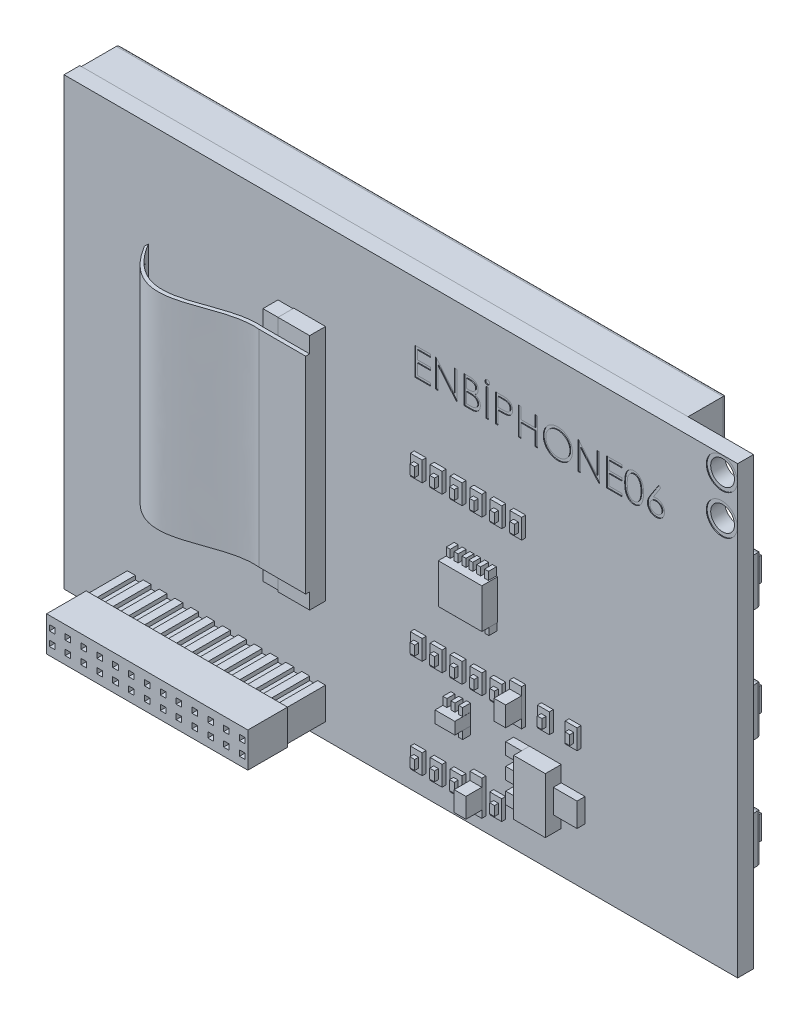
SolidWorks part; units mm, degrees
ref_plane "Front Plane" through (0, 0, 0) normal (0, 0, 1) x (1, 0, 0)
ref_plane "Top Plane" through (0, 0, 0) normal (0, 1, 0) x (1, 0, 0)
ref_plane "Right Plane" through (0, 0, 0) normal (1, 0, 0) x (0, 0, -1)
sketch "Sketch1" plane through (0, 0, 0) normal (0, 0, 1) x (1, 0, 0)
  line L0 (0, 0) -> (85.01, 0)
  line L1 (85.01, 0) -> (85.01, 56.21)
  line L2 (85.01, 56.21) -> (0, 56.21)
  line L3 (0, 56.21) -> (0, 0)
  dimension "D1" = 85.01
  dimension "D2" = 56.21
extrude "Boss-Extrude1" add sketch "Sketch1" along normal blind 2
sketch "Sketch2" plane through (0, 0, 2) normal (0, 0, 1) x (1, 0, 0)
  line L0 (85.01, 0) -> (85.01, 56.21) construction
  line L1 (85.01, 56.21) -> (0, 56.21) construction
  circle A1 centre (83.01, 54.21) radius 1.5
  circle A3 centre (83.01, 49.21) radius 1.5
  dimension "D4" = 3
  dimension "D6" = 3
  dimension "D2" = 2
  dimension "D3" = 2
  dimension "D5" = 5
extrude "Cut-Extrude1" cut sketch "Sketch2" against normal blind 2
sketch "Sketch4" plane through (0, 0, 2) normal (0, 0, 1) x (1, 0, 0)
  circle A0 centre (83.01, 54.21) radius 1.95
  circle A1 centre (83.01, 54.21) radius 1.5
  circle A2 centre (83.01, 49.21) radius 1.95
  circle A3 centre (83.01, 49.21) radius 1.5
  dimension "D1" = 3.9
  dimension "D2" = 3.9
extrude "Cut-Extrude7" cut sketch "Sketch4" against normal blind 0.1
sketch "Sketch5" plane through (0, 0, 0) normal (0, 0, -1) x (-1, 0, 0)
  circle A0 centre (-83.01, 54.21) radius 1.95
  circle A1 centre (-83.01, 49.21) radius 1.95
  circle A2 centre (-83.01, 54.21) radius 1.5
  circle A3 centre (-83.01, 49.21) radius 1.5
  dimension "D1" = 3.9
  dimension "D2" = 3.9
extrude "Cut-Extrude8" cut sketch "Sketch5" against normal blind 0.1
sketch "Sketch6" plane through (0, 0, 0) normal (0, 0, -1) x (-1, 0, 0)
  line L0 (-0.1, 56.11) -> (-0.1, 2.23)
  line L2 (-0.1, 2.23) -> (-76.65, 2.23)
  line L4 (-76.65, 2.23) -> (-76.65, 56.11)
  line L6 (-76.65, 56.11) -> (-0.1, 56.11)
  line L9 (-85.01, 56.21) -> (0, 56.21) construction
  line L10 (0, 56.21) -> (0, 0) construction
  line L11 (0, 0) -> (-85.01, 0) construction
  line L12 (-85.01, 0) -> (-85.01, 56.21) construction
  dimension "D1" = 0.1
  dimension "D2" = 0.1
  dimension "D3" = 2.23
  dimension "D4" = 8.36
extrude "Boss-Extrude2" add sketch "Sketch6" along normal blind 5
sketch "Sketch7" plane through (0, 0, -5) normal (0, 0, -1) x (-1, 0, 0)
  line L0 (-75.15, 54.71) -> (-1.5, 54.71)
  line L1 (-1.5, 54.71) -> (-1.5, 3.73)
  line L2 (-1.5, 3.73) -> (-75.15, 3.73)
  line L3 (-75.15, 3.73) -> (-75.15, 54.71)
  line L8 (-0.1, 56.11) -> (-76.65, 56.11) construction
  line L9 (-0.1, 2.23) -> (-0.1, 56.11) construction
  line L10 (-76.65, 2.23) -> (-0.1, 2.23) construction
  line L11 (-76.65, 56.11) -> (-76.65, 2.23) construction
  dimension "D1" = 1.4
  dimension "D2" = 1.4
  dimension "D3" = 1.5
  dimension "D4" = 1.5
extrude "Cut-Extrude9" cut sketch "Sketch7" against normal blind 0.1
fillet "Fillet1" radius 0.5 4 edges at (38.375, 2.23, -5) (76.65, 29.17, -5) (0.1, 29.17, -5) (38.375, 56.11, -5)
sketch "Sketch8" plane through (0, 0, 0) normal (0, 0, -1) x (-1, 0, 0)
  line L0 (-84.01, 10) -> (-81.01, 10)
  line L1 (-81.01, 10) -> (-81.01, 16)
  line L2 (-81.01, 16) -> (-84.01, 16)
  line L3 (-84.01, 16) -> (-84.01, 10)
  line L4 (-81.01, 24) -> (-84.01, 24)
  line L5 (-84.01, 24) -> (-84.01, 30)
  line L6 (-84.01, 30) -> (-81.01, 30)
  line L7 (-81.01, 30) -> (-81.01, 24)
  line L8 (-84.01, 44.21) -> (-84.01, 38.21)
  line L9 (-84.01, 38.21) -> (-81.01, 38.21)
  line L10 (-81.01, 38.21) -> (-81.01, 44.21)
  line L11 (-81.01, 44.21) -> (-84.01, 44.21)
  line L12 (0, 0) -> (-85.01, 0) construction
  line L13 (-85.01, 56.21) -> (0, 56.21) construction
  line L14 (-85.01, 0) -> (-85.01, 56.21) construction
  dimension "D1" = 6
  dimension "D2" = 6
  dimension "D3" = 6
  dimension "D4" = 10
  dimension "D5" = 12
  dimension "D6" = 8
  dimension "D7" = 1
  dimension "D8" = 1
  dimension "D9" = 3
  dimension "D10" = 3
  dimension "D11" = 3
extrude "Boss-Extrude3" add sketch "Sketch8" along normal blind 2
fillet "Fillet2" radius 0.5 12 edges at (81.01, 41.21, -2) (82.51, 38.21, -2) (84.01, 41.21, -2) (82.51, 44.21, -2) (82.51, 24, -2) (84.01, 27, -2) (82.51, 30, -2) (81.01, 27, -2) (82.51, 16, -2) (81.01, 13, -2) (82.51, 10, -2) (84.01, 13, -2)
sketch "Sketch9" plane through (0, 0, -2) normal (0, 0, -1) x (-1, 0, 0)
  line L0 (-83.01, 42.71) -> (-82.01, 42.71)
  line L1 (-82.01, 42.71) -> (-82.01, 39.71)
  line L2 (-82.01, 39.71) -> (-83.01, 39.71)
  line L3 (-83.01, 39.71) -> (-83.01, 42.71)
  line L4 (-83.51, 43.71) -> (-83.51, 38.71) construction
  line L5 (-83.51, 38.71) -> (-81.51, 38.71) construction
  line L6 (-83.01, 28.5) -> (-82.01, 28.5)
  line L7 (-82.01, 28.5) -> (-82.01, 25.5)
  line L8 (-82.01, 25.5) -> (-83.01, 25.5)
  line L9 (-83.01, 25.5) -> (-83.01, 28.5)
  line L10 (-83.51, 29.5) -> (-83.51, 24.5) construction
  line L11 (-81.51, 29.5) -> (-83.51, 29.5) construction
  line L12 (-83.01, 14.5) -> (-82.01, 14.5)
  line L13 (-82.01, 14.5) -> (-82.01, 11.5)
  line L14 (-82.01, 11.5) -> (-83.01, 11.5)
  line L15 (-83.01, 11.5) -> (-83.01, 14.5)
  line L16 (-83.51, 15.5) -> (-83.51, 10.5) construction
  line L17 (-81.51, 15.5) -> (-83.51, 15.5) construction
  point P6 (-82.51, 38.71)
  dimension "D1" = 1
  dimension "D2" = 3
  dimension "D3" = 0.5
  dimension "D4" = 1
  dimension "D5" = 1
  dimension "D6" = 3
  dimension "D7" = 0.5
  dimension "D8" = 1
  dimension "D9" = 1
  dimension "D10" = 3
  dimension "D11" = 0.5
  dimension "D12" = 1
extrude "Boss-Extrude4" add sketch "Sketch9" along normal blind 1
sketch "Sketch10" plane through (0, 0, 2) normal (0, 0, 1) x (1, 0, 0)
  line L0 (8, 2) -> (8, 6)
  line L1 (8, 2) -> (9, 2)
  line L2 (33, 6) -> (33, 2)
  line L3 (9, 2) -> (9, 2.5)
  line L5 (0, 56.21) -> (0, 0) construction
  line L6 (9, 2.5) -> (10, 2.5)
  line L7 (10, 2.5) -> (10, 2)
  line L8 (10, 2) -> (11, 2)
  line L9 (11, 2) -> (11, 2.5)
  line L10 (11, 2.5) -> (12, 2.5)
  line L11 (12, 2.5) -> (12, 2)
  line L12 (12, 2) -> (13, 2)
  line L13 (13, 2) -> (13, 2.5)
  line L14 (13, 2.5) -> (14, 2.5)
  line L15 (14, 2.5) -> (14, 2)
  line L16 (14, 2) -> (15, 2)
  line L17 (15, 2) -> (15, 2.5)
  line L18 (15, 2.5) -> (16, 2.5)
  line L19 (16, 2.5) -> (16, 2)
  line L20 (16, 2) -> (17, 2)
  line L21 (17, 2) -> (17, 2.5)
  line L22 (17, 2.5) -> (18, 2.5)
  line L23 (18, 2.5) -> (18, 2)
  line L24 (18, 2) -> (19, 2)
  line L25 (19, 2) -> (19, 2.5)
  line L26 (19, 2.5) -> (20, 2.5)
  line L27 (20, 2.5) -> (20, 2)
  line L28 (20, 2) -> (21, 2)
  line L29 (21, 2) -> (21, 2.5)
  line L30 (21, 2.5) -> (22, 2.5)
  line L31 (22, 2.5) -> (22, 2)
  line L32 (22, 2) -> (23, 2)
  line L33 (23, 2) -> (23, 2.5)
  line L34 (23, 2.5) -> (24, 2.5)
  line L35 (24, 2.5) -> (24, 2)
  line L36 (24, 2) -> (25, 2)
  line L37 (25, 2) -> (25, 2.5)
  line L38 (25, 2.5) -> (26, 2.5)
  line L39 (26, 2.5) -> (26, 2)
  line L40 (26, 2) -> (27, 2)
  line L41 (27, 2) -> (27, 2.5)
  line L42 (27, 2.5) -> (28, 2.5)
  line L43 (28, 2.5) -> (28, 2)
  line L44 (28, 2) -> (29, 2)
  line L45 (29, 2) -> (29, 2.5)
  line L46 (29, 2.5) -> (30, 2.5)
  line L47 (30, 2.5) -> (30, 2)
  line L48 (30, 2) -> (31, 2)
  line L49 (31, 2) -> (31, 2.5)
  line L50 (31, 2.5) -> (32, 2.5)
  line L51 (32, 2.5) -> (32, 2)
  line L52 (32, 2) -> (33, 2)
  line L54 (8, 4) -> (10, 4) construction
  line L55 (32, 5.5) -> (32, 6)
  line L56 (33, 2.5) -> (34, 2.5) [skipped]
  line L57 (34, 2.5) -> (34, 2) [skipped]
  line L58 (31, 5.5) -> (32, 5.5)
  line L59 (31, 6) -> (31, 5.5)
  line L60 (30, 6) -> (31, 6)
  line L61 (30, 5.5) -> (30, 6)
  line L62 (29, 5.5) -> (30, 5.5)
  line L63 (29, 6) -> (29, 5.5)
  line L64 (28, 6) -> (29, 6)
  line L65 (28, 5.5) -> (28, 6)
  line L66 (27, 5.5) -> (28, 5.5)
  line L67 (27, 6) -> (27, 5.5)
  line L68 (26, 6) -> (27, 6)
  line L69 (26, 5.5) -> (26, 6)
  line L70 (25, 5.5) -> (26, 5.5)
  line L71 (25, 6) -> (25, 5.5)
  line L72 (24, 6) -> (25, 6)
  line L73 (24, 5.5) -> (24, 6)
  line L74 (23, 5.5) -> (24, 5.5)
  line L75 (23, 6) -> (23, 5.5)
  line L76 (22, 6) -> (23, 6)
  line L77 (22, 5.5) -> (22, 6)
  line L78 (21, 5.5) -> (22, 5.5)
  line L79 (21, 6) -> (21, 5.5)
  line L80 (20, 6) -> (21, 6)
  line L81 (20, 5.5) -> (20, 6)
  line L82 (19, 5.5) -> (20, 5.5)
  line L83 (19, 6) -> (19, 5.5)
  line L84 (18, 6) -> (19, 6)
  line L85 (18, 5.5) -> (18, 6)
  line L86 (17, 5.5) -> (18, 5.5)
  line L87 (17, 6) -> (17, 5.5)
  line L88 (16, 6) -> (17, 6)
  line L89 (16, 5.5) -> (16, 6)
  line L90 (15, 5.5) -> (16, 5.5)
  line L91 (15, 6) -> (15, 5.5)
  line L92 (14, 6) -> (15, 6)
  line L93 (14, 5.5) -> (14, 6)
  line L94 (13, 5.5) -> (14, 5.5)
  line L95 (13, 6) -> (13, 5.5)
  line L96 (12, 6) -> (13, 6)
  line L97 (12, 5.5) -> (12, 6)
  line L98 (11, 5.5) -> (12, 5.5)
  line L99 (11, 6) -> (11, 5.5)
  line L100 (10, 6) -> (11, 6)
  line L101 (10, 5.5) -> (10, 6)
  line L102 (9, 5.5) -> (10, 5.5)
  line L103 (9, 6) -> (9, 5.5)
  line L104 (8, 6) -> (9, 6)
  line L105 (32, 6) -> (33, 6)
  line L107 (33, 2) -> (33, 2.5) [skipped]
  dimension "D2" = 8
  dimension "D3" = 25
  dimension "D4" = 4
  dimension "D5" = 1
  dimension "D6" = 0.5
  dimension "D7" = 0.5
  dimension "D8" = 13
extrude "Boss-Extrude5" add sketch "Sketch10" along normal blind 5
sketch "Sketch11" plane through (0, 0, 7) normal (0, 0, 1) x (1, 0, 0)
  line L0 (7.8, 6.2) -> (7.8, 1.8)
  line L1 (7.8, 1.8) -> (33.2, 1.8)
  line L2 (33.2, 1.8) -> (33.2, 6.2)
  line L3 (33.2, 6.2) -> (7.8, 6.2)
  line L4 (8, 6) -> (8, 2) construction
  line L5 (33, 2) -> (33, 6) construction
  line L6 (33, 6) -> (32, 6) construction
  line L7 (32, 2) -> (33, 2) construction
  line L8 (8.15, 5.2) -> (8.15, 4.5)
  line L9 (8.15, 4.5) -> (8.85, 4.5)
  line L10 (8.85, 4.5) -> (8.85, 5.2)
  line L11 (8.85, 5.2) -> (8.15, 5.2)
  line L12 (7.8, 4) -> (10.85, 4) construction
  line L13 (10.85, 5.2) -> (10.15, 5.2)
  line L14 (10.15, 5.2) -> (10.15, 4.5)
  line L15 (10.15, 4.5) -> (10.85, 4.5)
  line L16 (10.85, 4.5) -> (10.85, 5.2)
  line L17 (32.85, 3.5) -> (32.85, 2.8)
  line L18 (12.85, 5.2) -> (12.15, 5.2)
  line L19 (12.15, 5.2) -> (12.15, 4.5)
  line L20 (12.15, 4.5) -> (12.85, 4.5)
  line L21 (12.85, 4.5) -> (12.85, 5.2)
  line L22 (32.15, 3.5) -> (32.85, 3.5)
  line L23 (14.85, 5.2) -> (14.15, 5.2)
  line L24 (14.15, 5.2) -> (14.15, 4.5)
  line L25 (14.15, 4.5) -> (14.85, 4.5)
  line L26 (14.85, 4.5) -> (14.85, 5.2)
  line L27 (32.15, 2.8) -> (32.15, 3.5)
  line L28 (16.85, 5.2) -> (16.15, 5.2)
  line L29 (16.15, 5.2) -> (16.15, 4.5)
  line L30 (16.15, 4.5) -> (16.85, 4.5)
  line L31 (16.85, 4.5) -> (16.85, 5.2)
  line L32 (32.85, 2.8) -> (32.15, 2.8)
  line L33 (18.85, 5.2) -> (18.15, 5.2)
  line L34 (18.15, 5.2) -> (18.15, 4.5)
  line L35 (18.15, 4.5) -> (18.85, 4.5)
  line L36 (18.85, 4.5) -> (18.85, 5.2)
  line L37 (30.85, 3.5) -> (30.85, 2.8)
  line L38 (20.85, 5.2) -> (20.15, 5.2)
  line L39 (20.15, 5.2) -> (20.15, 4.5)
  line L40 (20.15, 4.5) -> (20.85, 4.5)
  line L41 (20.85, 4.5) -> (20.85, 5.2)
  line L42 (30.15, 3.5) -> (30.85, 3.5)
  line L43 (22.85, 5.2) -> (22.15, 5.2)
  line L44 (22.15, 5.2) -> (22.15, 4.5)
  line L45 (22.15, 4.5) -> (22.85, 4.5)
  line L46 (22.85, 4.5) -> (22.85, 5.2)
  line L47 (30.15, 2.8) -> (30.15, 3.5)
  line L48 (24.85, 5.2) -> (24.15, 5.2)
  line L49 (24.15, 5.2) -> (24.15, 4.5)
  line L50 (24.15, 4.5) -> (24.85, 4.5)
  line L51 (24.85, 4.5) -> (24.85, 5.2)
  line L52 (30.85, 2.8) -> (30.15, 2.8)
  line L53 (26.85, 5.2) -> (26.15, 5.2)
  line L54 (26.15, 5.2) -> (26.15, 4.5)
  line L55 (26.15, 4.5) -> (26.85, 4.5)
  line L56 (26.85, 4.5) -> (26.85, 5.2)
  line L57 (28.85, 3.5) -> (28.85, 2.8)
  line L58 (28.85, 5.2) -> (28.15, 5.2)
  line L59 (28.15, 5.2) -> (28.15, 4.5)
  line L60 (28.15, 4.5) -> (28.85, 4.5)
  line L61 (28.85, 4.5) -> (28.85, 5.2)
  line L62 (28.15, 3.5) -> (28.85, 3.5)
  line L63 (30.85, 5.2) -> (30.15, 5.2)
  line L64 (30.15, 5.2) -> (30.15, 4.5)
  line L65 (30.15, 4.5) -> (30.85, 4.5)
  line L66 (30.85, 4.5) -> (30.85, 5.2)
  line L67 (28.15, 2.8) -> (28.15, 3.5)
  line L68 (32.85, 5.2) -> (32.15, 5.2)
  line L69 (32.15, 5.2) -> (32.15, 4.5)
  line L70 (32.15, 4.5) -> (32.85, 4.5)
  line L71 (32.85, 4.5) -> (32.85, 5.2)
  line L72 (39.2, 6.2) -> (13.8, 6.2) [skipped]
  line L73 (41.2, 6.2) -> (15.8, 6.2) [skipped]
  line L74 (43.2, 6.2) -> (17.8, 6.2) [skipped]
  line L75 (45.2, 6.2) -> (19.8, 6.2) [skipped]
  line L76 (47.2, 6.2) -> (21.8, 6.2) [skipped]
  line L77 (49.2, 6.2) -> (23.8, 6.2) [skipped]
  line L78 (51.2, 6.2) -> (25.8, 6.2) [skipped]
  line L79 (53.2, 6.2) -> (27.8, 6.2) [skipped]
  line L80 (55.2, 6.2) -> (29.8, 6.2) [skipped]
  line L81 (57.2, 6.2) -> (31.8, 6.2) [skipped]
  line L82 (37.2, 6.2) -> (11.8, 6.2) [skipped]
  line L83 (35.2, 6.2) -> (9.8, 6.2) [skipped]
  line L84 (28.85, 2.8) -> (28.15, 2.8)
  line L85 (26.85, 3.5) -> (26.85, 2.8)
  line L86 (26.15, 3.5) -> (26.85, 3.5)
  line L87 (26.15, 2.8) -> (26.15, 3.5)
  line L88 (26.85, 2.8) -> (26.15, 2.8)
  line L89 (24.85, 3.5) -> (24.85, 2.8)
  line L90 (24.15, 3.5) -> (24.85, 3.5)
  line L91 (24.15, 2.8) -> (24.15, 3.5)
  line L92 (24.85, 2.8) -> (24.15, 2.8)
  line L93 (22.85, 3.5) -> (22.85, 2.8)
  line L94 (22.15, 3.5) -> (22.85, 3.5)
  line L95 (22.15, 2.8) -> (22.15, 3.5)
  line L96 (22.85, 2.8) -> (22.15, 2.8)
  line L97 (20.85, 3.5) -> (20.85, 2.8)
  line L98 (20.15, 3.5) -> (20.85, 3.5)
  line L99 (20.15, 2.8) -> (20.15, 3.5)
  line L100 (20.85, 2.8) -> (20.15, 2.8)
  line L101 (18.85, 3.5) -> (18.85, 2.8)
  line L102 (18.15, 3.5) -> (18.85, 3.5)
  line L103 (18.15, 2.8) -> (18.15, 3.5)
  line L104 (18.85, 2.8) -> (18.15, 2.8)
  line L105 (16.85, 3.5) -> (16.85, 2.8)
  line L106 (16.15, 3.5) -> (16.85, 3.5)
  line L107 (16.15, 2.8) -> (16.15, 3.5)
  line L108 (16.85, 2.8) -> (16.15, 2.8)
  line L109 (14.85, 3.5) -> (14.85, 2.8)
  line L110 (14.15, 3.5) -> (14.85, 3.5)
  line L111 (14.15, 2.8) -> (14.15, 3.5)
  line L112 (14.85, 2.8) -> (14.15, 2.8)
  line L113 (12.85, 3.5) -> (12.85, 2.8)
  line L114 (12.15, 3.5) -> (12.85, 3.5)
  line L115 (12.15, 2.8) -> (12.15, 3.5)
  line L116 (12.85, 2.8) -> (12.15, 2.8)
  line L117 (10.85, 3.5) -> (10.85, 2.8)
  line L118 (10.15, 3.5) -> (10.85, 3.5)
  line L119 (10.15, 2.8) -> (10.15, 3.5)
  line L120 (10.85, 2.8) -> (10.15, 2.8)
  line L121 (8.85, 2.8) -> (8.15, 2.8)
  line L122 (8.85, 3.5) -> (8.85, 2.8)
  line L123 (8.15, 3.5) -> (8.85, 3.5)
  line L124 (8.15, 2.8) -> (8.15, 3.5)
  dimension "D1" = 0.2
  dimension "D2" = 0.2
  dimension "D3" = 0.2
  dimension "D4" = 0.2
  dimension "D5" = 0.7
  dimension "D6" = 0.7
  dimension "D7" = 0.35
  dimension "D8" = 1
  dimension "D9" = 13
extrude "Boss-Extrude6" add sketch "Sketch11" along normal blind 5
sketch "Sketch13" plane through (0, 0, 2) normal (0, 0, 1) x (1, 0, 0)
  line L0 (44.2, 5.2) -> (44.2, 2.7)
  line L1 (44.2, 2.7) -> (45.7, 2.7)
  line L2 (45.7, 2.7) -> (45.7, 5.2)
  line L3 (45.7, 5.2) -> (44.2, 5.2)
  line L4 (33.2, 6.2) -> (7.8, 6.2) construction
  line L5 (53.2275, 37.2171) -> (51.7275, 37.2171)
  line L6 (33.2, 1.8) -> (33.2, 6.2) construction
  line L7 (48.2138, 5.2) -> (46.7138, 5.2)
  line L8 (46.7138, 5.2) -> (46.7138, 2.7)
  line L9 (46.7138, 2.7) -> (48.2138, 2.7)
  line L10 (48.2138, 2.7) -> (48.2138, 5.2)
  line L11 (50.7275, 5.2) -> (49.2275, 5.2)
  line L12 (49.2275, 5.2) -> (49.2275, 2.7)
  line L13 (49.2275, 2.7) -> (50.7275, 2.7)
  line L14 (50.7275, 2.7) -> (50.7275, 5.2)
  line L15 (51.7275, 6.2) -> (51.7275, 1.8)
  line L16 (51.7275, 1.8) -> (53.2275, 1.8)
  line L17 (53.2275, 1.8) -> (53.2275, 6.2)
  line L18 (53.2275, 6.2) -> (51.7275, 6.2)
  line L19 (7.8, 1.8) -> (33.2, 1.8) construction
  line L20 (54.2275, 5.2) -> (54.2275, 2.7)
  line L21 (54.2275, 2.7) -> (55.7275, 2.7)
  line L22 (55.7275, 2.7) -> (55.7275, 5.2)
  line L23 (55.7275, 5.2) -> (54.2275, 5.2)
  line L24 (49.2275, 15.2) -> (50.7275, 15.2)
  line L25 (48.2138, 15.2) -> (48.2138, 17.7)
  line L26 (45.7, 15.2) -> (45.7, 17.7)
  line L27 (50.7275, 15.2) -> (50.7275, 17.7)
  line L28 (44.2, 17.7) -> (44.2, 15.2)
  line L29 (50.7275, 17.7) -> (49.2275, 17.7)
  line L30 (46.7138, 17.7) -> (46.7138, 15.2)
  line L31 (48.2138, 17.7) -> (46.7138, 17.7)
  line L32 (44.2, 15.2) -> (45.7, 15.2)
  line L33 (49.2275, 17.7) -> (49.2275, 15.2)
  line L34 (45.7, 17.7) -> (44.2, 17.7)
  line L35 (46.7138, 15.2) -> (48.2138, 15.2)
  line L36 (51.7275, 15.2) -> (53.2275, 15.2)
  line L37 (55.7413, 15.2) -> (55.7413, 17.7)
  line L38 (54.2413, 15.2) -> (55.7413, 15.2)
  line L39 (53.2275, 17.7) -> (51.7275, 17.7)
  line L40 (51.7275, 17.7) -> (51.7275, 15.2)
  line L41 (53.2275, 15.2) -> (53.2275, 17.7)
  line L42 (55.7413, 17.7) -> (54.2413, 17.7)
  line L43 (54.2413, 17.7) -> (54.2413, 15.2)
  line L44 (56.7413, 18.7) -> (56.7413, 14.0831)
  line L45 (58.2413, 14.0831) -> (58.2413, 18.7)
  line L46 (56.7413, 14.0831) -> (58.2413, 14.0831)
  line L47 (58.2413, 18.7) -> (56.7413, 18.7)
  line L48 (61.7413, 17.7) -> (60.2413, 17.7)
  line L49 (61.7413, 15.2) -> (61.7413, 17.7)
  line L50 (60.2413, 17.7) -> (60.2413, 15.2)
  line L51 (60.2413, 15.2) -> (61.7413, 15.2)
  line L52 (65.2413, 15.2) -> (65.2413, 17.7)
  line L53 (65.2413, 17.7) -> (63.7413, 17.7)
  line L54 (63.7413, 15.2) -> (65.2413, 15.2)
  line L55 (63.7413, 17.7) -> (63.7413, 15.2)
  line L56 (54.2413, 37.2171) -> (54.2413, 34.7171)
  line L57 (55.7413, 34.7171) -> (55.7413, 37.2171)
  line L58 (54.2413, 34.7171) -> (55.7413, 34.7171)
  line L59 (51.7275, 34.7171) -> (53.2275, 34.7171)
  line L60 (46.7138, 37.2171) -> (46.7138, 34.7171)
  line L61 (48.2138, 34.7171) -> (48.2138, 37.2171)
  line L62 (55.7413, 37.2171) -> (54.2413, 37.2171)
  line L63 (50.7275, 34.7171) -> (50.7275, 37.2171)
  line L64 (44.2, 34.7) -> (45.7, 34.7)
  line L65 (50.7275, 37.2171) -> (49.2275, 37.2171)
  line L66 (45.7, 37.2) -> (44.2, 37.2)
  line L67 (51.7275, 37.2171) -> (51.7275, 34.7171)
  line L68 (46.7138, 34.7171) -> (48.2138, 34.7171)
  line L69 (49.2275, 34.7171) -> (50.7275, 34.7171)
  line L70 (53.2275, 34.7171) -> (53.2275, 37.2171)
  line L71 (45.7, 34.7) -> (45.7, 37.2)
  line L72 (48.2138, 37.2171) -> (46.7138, 37.2171)
  line L73 (44.2, 37.2) -> (44.2, 34.7)
  line L74 (49.2275, 37.2171) -> (49.2275, 34.7171)
  line L75 (58.2551, 34.7171) -> (58.2551, 37.2171)
  line L76 (58.2551, 37.2171) -> (56.7551, 37.2171)
  line L77 (56.7551, 37.2171) -> (56.7551, 34.7171)
  line L78 (56.7551, 34.7171) -> (58.2551, 34.7171)
  dimension "D1" = 1.5
  dimension "D2" = 2.5
  dimension "D3" = 1
  dimension "D4" = 11
  dimension "D6" = 1.5
  dimension "D7" = 1
  dimension "D8" = 0
  dimension "D9" = 0
  dimension "D10" = 1.5
  dimension "D11" = 2.5
  dimension "D12" = 1
  dimension "D13" = 2.5
  dimension "D14" = 1
  dimension "D15" = 1
  dimension "D16" = 2
  dimension "D17" = 2
  dimension "D18" = 10
  dimension "D19" = 17
  dimension "D5" = 3
extrude "Boss-Extrude7" add sketch "Sketch13" along normal blind 0.5
sketch "Sketch16" plane through (0, 0, 2.5) normal (0, 0, 1) x (1, 0, 0)
  line L0 (44.65, 4.5) -> (44.65, 3.3)
  line L1 (44.65, 3.3) -> (45.25, 3.3)
  line L2 (45.25, 3.3) -> (45.25, 4.5)
  line L3 (45.25, 4.5) -> (44.65, 4.5)
  line L4 (44.2, 5.2) -> (44.2, 2.7) construction
  line L5 (44.2, 2.7) -> (45.7, 2.7) construction
  line L6 (47.15, 3.3) -> (47.75, 3.3)
  line L7 (47.75, 3.3) -> (47.75, 4.5)
  line L8 (47.15, 4.5) -> (47.15, 3.3)
  line L9 (47.75, 4.5) -> (47.15, 4.5)
  line L10 (49.65, 3.3) -> (50.25, 3.3)
  line L11 (50.25, 3.3) -> (50.25, 4.5)
  line L12 (49.65, 4.5) -> (49.65, 3.3)
  line L13 (50.25, 4.5) -> (49.65, 4.5)
  line L14 (55.3202, 15.8) -> (55.3202, 17)
  line L15 (54.7202, 17) -> (54.7202, 15.8)
  line L16 (45.25, 17) -> (44.65, 17)
  line L17 (49.65, 15.8) -> (50.25, 15.8)
  line L18 (54.7202, 3.3) -> (55.3202, 3.3)
  line L19 (55.3202, 4.5) -> (54.7202, 4.5)
  line L20 (55.3202, 3.3) -> (55.3202, 4.5)
  line L21 (54.7202, 4.5) -> (54.7202, 3.3)
  line L22 (47.75, 15.8) -> (47.75, 17)
  line L23 (50.25, 17) -> (49.65, 17)
  line L24 (47.75, 17) -> (47.15, 17)
  line L25 (55.3202, 17) -> (54.7202, 17)
  line L26 (44.65, 17) -> (44.65, 15.8)
  line L27 (44.65, 15.8) -> (45.25, 15.8)
  line L28 (45.25, 15.8) -> (45.25, 17)
  line L29 (49.65, 17) -> (49.65, 15.8)
  line L30 (47.15, 15.8) -> (47.75, 15.8)
  line L31 (50.25, 15.8) -> (50.25, 17)
  line L32 (47.15, 17) -> (47.15, 15.8)
  line L33 (54.7202, 15.8) -> (55.3202, 15.8)
  line L34 (52.75, 15.8) -> (52.75, 17)
  line L35 (52.15, 15.8) -> (52.75, 15.8)
  line L36 (52.75, 17) -> (52.15, 17)
  line L37 (52.15, 17) -> (52.15, 15.8)
  line L38 (60.7202, 17) -> (60.7202, 15.8)
  line L39 (61.3202, 17) -> (60.7202, 17)
  line L40 (60.7202, 15.8) -> (61.3202, 15.8)
  line L41 (61.3202, 15.8) -> (61.3202, 17)
  line L42 (64.2202, 17) -> (64.2202, 15.8)
  line L43 (64.8202, 17) -> (64.2202, 17)
  line L44 (64.2202, 15.8) -> (64.8202, 15.8)
  line L45 (64.8202, 15.8) -> (64.8202, 17)
  line L46 (55.3202, 36.5) -> (54.7202, 36.5)
  line L47 (52.15, 36.5) -> (52.15, 35.3)
  line L48 (55.3202, 35.3) -> (55.3202, 36.5)
  line L49 (52.75, 36.5) -> (52.15, 36.5)
  line L50 (44.65, 36.5) -> (44.65, 35.3)
  line L51 (45.25, 36.5) -> (44.65, 36.5)
  line L52 (49.65, 35.3) -> (50.25, 35.3)
  line L53 (54.7202, 35.3) -> (55.3202, 35.3)
  line L54 (47.75, 36.5) -> (47.15, 36.5)
  line L55 (47.15, 35.3) -> (47.75, 35.3)
  line L56 (52.75, 35.3) -> (52.75, 36.5)
  line L57 (52.15, 35.3) -> (52.75, 35.3)
  line L58 (45.25, 35.3) -> (45.25, 36.5)
  line L59 (44.65, 35.3) -> (45.25, 35.3)
  line L60 (54.7202, 36.5) -> (54.7202, 35.3)
  line L61 (50.25, 36.5) -> (49.65, 36.5)
  line L62 (47.15, 36.5) -> (47.15, 35.3)
  line L63 (50.25, 35.3) -> (50.25, 36.5)
  line L64 (47.75, 35.3) -> (47.75, 36.5)
  line L65 (49.65, 36.5) -> (49.65, 35.3)
  line L66 (57.8339, 36.5) -> (57.2339, 36.5)
  line L67 (57.2339, 35.3) -> (57.8339, 35.3)
  line L68 (57.2339, 36.5) -> (57.2339, 35.3)
  line L69 (57.8339, 35.3) -> (57.8339, 36.5)
  dimension "D1" = 0.6
  dimension "D2" = 1.2
  dimension "D3" = 0.45
  dimension "D4" = 0.6
  dimension "D5" = 3
extrude "Boss-Extrude8" add sketch "Sketch16" along normal blind 0.5
sketch "Sketch17" plane through (0, 0, 2.5) normal (0, 0, 1) x (1, 0, 0)
  line L0 (51.7375, 5.2) -> (53.2175, 5.2)
  line L3 (53.2175, 5.2) -> (53.2175, 2.7)
  line L5 (53.2175, 2.7) -> (51.7375, 2.7)
  line L7 (51.7375, 2.7) -> (51.7375, 5.2)
  line L8 (51.7275, 6.2) -> (51.7275, 1.8) construction
  line L9 (53.2275, 1.8) -> (53.2275, 6.2) construction
  line L10 (58.2313, 15.2) -> (56.7513, 15.2)
  line L11 (58.2313, 17.7) -> (58.2313, 15.2)
  line L12 (56.7513, 15.2) -> (56.7513, 17.7)
  line L13 (56.7513, 17.7) -> (58.2313, 17.7)
  dimension "D1" = 0.01
  dimension "D2" = 0.01
extrude "Boss-Extrude9" add sketch "Sketch17" along normal blind 2
sketch "Sketch19" plane through (0, 0, 2) normal (0, 0, 1) x (1, 0, 0)
  line L0 (58.7413, 5.2) -> (58.7413, 12.2)
  line L1 (58.7413, 12.2) -> (62.7413, 12.2)
  line L2 (62.7413, 12.2) -> (62.7413, 5.2)
  line L3 (62.7413, 5.2) -> (58.7413, 5.2)
  line L4 (58.2413, 14.0831) -> (58.2413, 18.7) construction
  line L5 (48.8163, 12.2) -> (51.3163, 12.2)
  line L6 (51.3163, 12.2) -> (51.3163, 10.7)
  line L7 (51.3163, 10.7) -> (48.8163, 10.7)
  line L8 (48.8163, 10.7) -> (48.8163, 12.2)
  line L9 (49.2275, 28.7171) -> (49.2275, 23.7171)
  line L10 (49.2275, 23.7171) -> (54.7275, 23.7171)
  line L11 (54.7275, 23.7171) -> (54.7275, 28.7171)
  line L12 (54.7275, 28.7171) -> (49.2275, 28.7171)
  line L13 (49.2275, 34.7171) -> (50.7275, 34.7171) construction
  dimension "D1" = 4
  dimension "D2" = 0.5
  dimension "D3" = 7
  dimension "D4" = 1.5
  dimension "D5" = 2.5
  dimension "D6" = 5.5
  dimension "D7" = 5
  dimension "D8" = 6
extrude "Boss-Extrude10" add sketch "Sketch19" along normal blind 2
sketch "Sketch21" plane through (0, 0, 2) normal (0, 0, 1) x (1, 0, 0)
  line L0 (48.8263, 12.2) -> (48.8263, 13.2)
  line L1 (51.3163, 12.2) -> (48.8163, 12.2) construction
  line L2 (48.8263, 13.2) -> (49.3263, 13.2)
  line L3 (49.3263, 13.2) -> (49.3263, 12.2)
  line L4 (49.3263, 12.2) -> (48.8263, 12.2)
  line L5 (48.8163, 12.2) -> (48.8163, 10.7) construction
  line L6 (50.3263, 13.2) -> (50.3263, 12.2)
  line L7 (49.8263, 13.2) -> (50.3263, 13.2)
  line L8 (49.8263, 12.2) -> (49.8263, 13.2)
  line L9 (50.3263, 12.2) -> (49.8263, 12.2)
  line L11 (51.3063, 12.2) -> (50.8063, 12.2)
  line L12 (50.8063, 12.2) -> (50.8063, 13.2)
  line L13 (50.8063, 13.2) -> (51.3063, 13.2)
  line L14 (51.3063, 13.2) -> (51.3063, 12.2)
  line L15 (51.3163, 10.7) -> (51.3163, 12.2) construction
  line L16 (48.8163, 11.45) -> (50.8937, 11.45) construction
  line L17 (51.3063, 9.7) -> (51.3063, 10.7)
  line L18 (50.8063, 9.7) -> (51.3063, 9.7)
  line L19 (50.8063, 10.7) -> (50.8063, 9.7)
  line L20 (51.3063, 10.7) -> (50.8063, 10.7)
  line L21 (50.3263, 10.7) -> (49.8263, 10.7)
  line L22 (49.8263, 10.7) -> (49.8263, 9.7)
  line L23 (49.8263, 9.7) -> (50.3263, 9.7)
  line L24 (50.3263, 9.7) -> (50.3263, 10.7)
  line L25 (49.3263, 10.7) -> (48.8263, 10.7)
  line L26 (49.3263, 9.7) -> (49.3263, 10.7)
  line L27 (48.8263, 9.7) -> (49.3263, 9.7)
  line L28 (48.8263, 10.7) -> (48.8263, 9.7)
  line L29 (50.2375, 29.7171) -> (50.7375, 29.7171)
  line L30 (49.2375, 28.7171) -> (49.2375, 29.7171)
  line L31 (51.2175, 29.7171) -> (51.7175, 29.7171)
  line L32 (50.7375, 29.7171) -> (50.7375, 28.7171)
  line L33 (51.7175, 29.7171) -> (51.7175, 28.7171)
  line L34 (49.7375, 28.7171) -> (49.2375, 28.7171)
  line L35 (49.2375, 29.7171) -> (49.7375, 29.7171)
  line L36 (51.7175, 28.7171) -> (51.2175, 28.7171)
  line L37 (49.7375, 29.7171) -> (49.7375, 28.7171)
  line L38 (50.7375, 28.7171) -> (50.2375, 28.7171)
  line L39 (50.2375, 28.7171) -> (50.2375, 29.7171)
  line L40 (51.2175, 28.7171) -> (51.2175, 29.7171)
  line L41 (53.0814, 29.7171) -> (53.5814, 29.7171)
  line L42 (52.0814, 28.7171) -> (52.0814, 29.7171)
  line L43 (54.0614, 29.7171) -> (54.5614, 29.7171)
  line L44 (53.5814, 29.7171) -> (53.5814, 28.7171)
  line L45 (54.5614, 29.7171) -> (54.5614, 28.7171)
  line L46 (52.5814, 28.7171) -> (52.0814, 28.7171)
  line L47 (52.0814, 29.7171) -> (52.5814, 29.7171)
  line L48 (54.5614, 28.7171) -> (54.0614, 28.7171)
  line L49 (52.5814, 29.7171) -> (52.5814, 28.7171)
  line L50 (53.5814, 28.7171) -> (53.0814, 28.7171)
  line L51 (53.0814, 28.7171) -> (53.0814, 29.7171)
  line L52 (54.0614, 28.7171) -> (54.0614, 29.7171)
  line L53 (51.7713, 23.715) -> (51.7713, 22.715)
  line L54 (52.1351, 22.715) -> (52.1351, 23.715)
  line L55 (53.1351, 22.715) -> (53.1351, 23.715)
  line L56 (51.7713, 22.715) -> (51.2713, 22.715)
  line L57 (54.1151, 23.715) -> (54.6151, 23.715)
  line L58 (52.1351, 23.715) -> (52.6351, 23.715)
  line L59 (53.1351, 23.715) -> (53.6351, 23.715)
  line L60 (53.6351, 23.715) -> (53.6351, 22.715)
  line L61 (50.7913, 22.715) -> (50.2913, 22.715)
  line L62 (49.7913, 22.715) -> (49.2913, 22.715)
  line L63 (49.2913, 23.715) -> (49.7913, 23.715)
  line L64 (53.6351, 22.715) -> (53.1351, 22.715)
  line L65 (50.2913, 23.715) -> (50.7913, 23.715)
  line L66 (49.2913, 22.715) -> (49.2913, 23.715)
  line L67 (52.6351, 23.715) -> (52.6351, 22.715)
  line L68 (49.7913, 23.715) -> (49.7913, 22.715)
  line L69 (50.2913, 22.715) -> (50.2913, 23.715)
  line L70 (54.6151, 23.715) -> (54.6151, 22.715)
  line L71 (54.6151, 22.715) -> (54.1151, 22.715)
  line L72 (50.7913, 23.715) -> (50.7913, 22.715)
  line L73 (52.6351, 22.715) -> (52.1351, 22.715)
  line L74 (54.1151, 22.715) -> (54.1151, 23.715)
  line L75 (51.2713, 23.715) -> (51.7713, 23.715)
  line L76 (51.2713, 22.715) -> (51.2713, 23.715)
  line L77 (62.7413, 10.2) -> (65.7413, 10.2)
  line L78 (62.7413, 5.2) -> (62.7413, 12.2) construction
  line L79 (65.7413, 10.2) -> (65.7413, 7.2)
  line L80 (65.7413, 7.2) -> (62.7413, 7.2)
  line L81 (62.7413, 7.2) -> (62.7413, 10.2)
  line L82 (58.7413, 12.19) -> (56.7413, 12.19)
  line L83 (58.7413, 12.2) -> (58.7413, 5.2) construction
  line L84 (56.7413, 12.19) -> (56.7413, 10.69)
  line L85 (56.7413, 10.69) -> (58.7413, 10.69)
  line L86 (58.7413, 10.69) -> (58.7413, 12.19)
  line L87 (62.7413, 12.2) -> (58.7413, 12.2) construction
  line L88 (62.7413, 12.2) -> (58.7413, 12.2) construction
  line L89 (58.7413, 9.49) -> (56.7413, 9.49)
  line L90 (56.7413, 9.49) -> (56.7413, 7.99)
  line L91 (56.7413, 7.99) -> (58.7413, 7.99)
  line L92 (58.7413, 7.99) -> (58.7413, 9.49)
  line L93 (58.7413, 6.79) -> (56.7413, 6.79)
  line L94 (56.7413, 6.79) -> (56.7413, 5.29)
  line L95 (56.7413, 5.29) -> (58.7413, 5.29)
  line L96 (58.7413, 5.29) -> (58.7413, 6.79)
  dimension "D1" = 0.01
  dimension "D2" = 0.5
  dimension "D3" = 1
  dimension "D5" = 0.01
  dimension "D6" = 0.5
  dimension "D7" = 1
  dimension "D8" = 0.5
  dimension "D9" = 1
  dimension "D10" = 0.5
  dimension "D11" = 1
  dimension "D12" = 0.5
  dimension "D13" = 1
  dimension "D14" = 0.5
  dimension "D15" = 0.01
  dimension "D16" = 1.5
  dimension "D17" = 2
  dimension "D18" = 3
  dimension "D19" = 3
  dimension "D20" = 2
  dimension "D4" = 2
  dimension "D21" = 3
extrude "Boss-Extrude12" add sketch "Sketch21" along normal blind 1
sketch "Sketch22" plane through (0, 0, 2) normal (0, 0, 1) x (1, 0, 0)
  line L0 (33, 15.2) -> (33, 45.2)
  line L1 (33, 45.2) -> (29, 45.2)
  line L2 (29, 45.2) -> (29, 15.2)
  line L3 (29, 15.2) -> (33, 15.2)
  dimension "D1" = 4
  dimension "D2" = 30
extrude "Boss-Extrude13" add sketch "Sketch22" along normal blind 2
sketch "Sketch23" plane through (0, 0, 2) normal (0, 0, 1) x (1, 0, 0)
  line L0 (29, 45.1) -> (27, 45.1)
  line L1 (29, 45.2) -> (29, 15.2) construction
  line L2 (27, 45.1) -> (27, 15.3)
  line L3 (27, 15.3) -> (29, 15.3)
  line L4 (29, 15.3) -> (29, 45.1)
  line L5 (33, 45.2) -> (29, 45.2) construction
  line L6 (29, 15.2) -> (33, 15.2) construction
  dimension "D1" = 0.1
  dimension "D2" = 0.1
  dimension "D3" = 2
extrude "Boss-Extrude14" add sketch "Sketch23" along normal blind 1.9
sketch "Sketch25" plane through (0, 0, 4) normal (0, 0, 1) x (1, 0, 0)
  line L0 (33, 43.2) -> (27.1, 43.2)
  line L1 (33, 15.2) -> (33, 45.2) construction
  line L2 (27.1, 43.2) -> (27.1, 17.2)
  line L3 (27.1, 17.2) -> (33, 17.2)
  line L4 (33, 17.2) -> (33, 43.2)
  line L5 (33, 45.2) -> (29, 45.2) construction
  line L6 (29, 15.2) -> (33, 15.2) construction
  line L7 (27, 45.1) -> (27, 15.3) construction
  dimension "D1" = 2
  dimension "D2" = 2
  dimension "D3" = 0.1
extrude "Boss-Extrude15" add sketch "Sketch25" along normal blind 0.5
sketch "Sketch26" plane through (0, 43.2, 0) normal (0, 1, 0) x (1, 0, 0)
  line L0 (27.1, -4.5) -> (27.1, -4) construction
  line L1 (27.1, -4.5) -> (27.1, -4)
  line L2 (10.8024, -2.664) -> (10.8024, -2.164)
  spline S0 degree 3 poles (27.1, -4) (21.204, -3.4486) (15.8584, -10.5256) (10.8024, -2.164) knots 0 0 0 0 1 1 1 1
  spline S1 degree 3 poles (27.1, -4.5) (21.204, -3.9486) (15.8584, -11.0256) (10.8024, -2.664) knots 0 0 0 0 1 1 1 1
extrude "Boss-Extrude16" add sketch "Sketch26" against normal blind 26
sketch "Sketch28" plane through (0, 0, 2) normal (0, 0, 1) x (1, 0, 0)
  text T0 "ENBİPHONE06"
extrude "Cut-Extrude10" cut sketch "Sketch28" against normal blind 0.1
